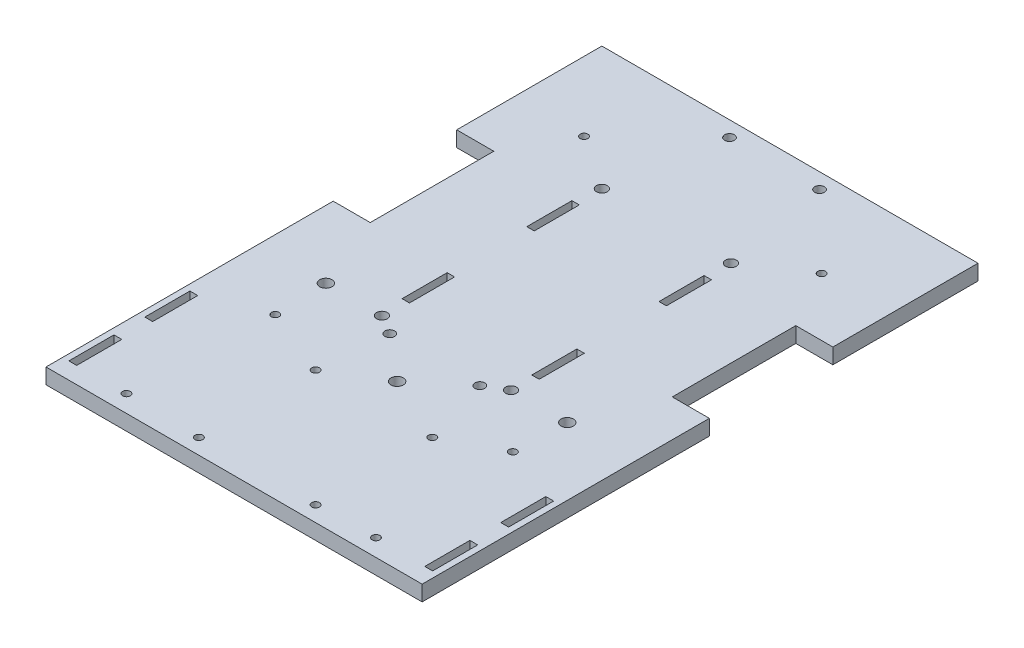
SolidWorks part; units mm, degrees
ref_plane "Front Plane" through (0, 0, 0) normal (0, 0, 1) x (1, 0, 0)
ref_plane "Top Plane" through (0, 0, 0) normal (0, 1, 0) x (1, 0, 0)
ref_plane "Right Plane" through (0, 0, 0) normal (1, 0, 0) x (0, 0, -1)
sketch "Sketch1" plane through (0, 0, 0) normal (0, 1, 0) x (1, 0, 0)
  circle A0 centre (0, 90.4441) radius 2.2225
  circle A1 centre (53.086, 90.4441) radius 2.2225
  circle A2 centre (0, 0) radius 2.2225
  circle A3 centre (53.086, 0) radius 2.2225
  dimension "D1" = 4.445
  dimension "D2" = 4.445
  dimension "D3" = 4.445
  dimension "D4" = 4.445
  dimension "D5" = 53.086
  dimension "D6" = 90.4441
  dimension "D7" = 104.8725
  dimension "D8" = 0
  dimension "D10" = 104.8725
  dimension "D11" = 53.086
  dimension "D9" = 53.086
sketch "Sketch2" plane through (0, 0, 0) normal (0, 1, 0) x (1, 0, 0)
  line L1 (-50.8, 141.2441) -> (103.886, 141.2441)
  line L2 (-50.8, 141.2441) -> (-50.8, -87.3559)
  line L3 (-50.8, -87.3559) -> (103.886, -87.3559)
  line L4 (103.886, 141.2441) -> (103.886, -87.3559)
  circle A0 centre (0, 90.4441) radius 2.2225 construction
  circle A1 centre (53.086, 90.4441) radius 2.2225 construction
  dimension "D3" = 50.8
  dimension "D1" = 50.8
  dimension "D2" = 50.8
  dimension "D4" = 228.6
extrude "Boss-Extrude1" add sketch "Sketch2" along normal blind 6.35
extrude "Cut-Extrude1" cut sketch "Sketch1" along normal blind 6.35
sketch "Sketch3" plane through (0, 6.35, 0) normal (0, 1, 0) x (1, 0, 0)
  line L0 (103.886, -87.3559) -> (103.886, 141.2441) construction
  line L1 (103.886, 81.5541) -> (88.646, 81.5541)
  line L2 (103.886, 81.5541) -> (103.886, 30.7541)
  line L3 (103.886, 30.7541) -> (88.646, 30.7541)
  line L4 (88.646, 81.5541) -> (88.646, 30.7541)
  line L5 (-50.8, 141.2441) -> (-50.8, -87.3559) construction
  line L6 (-50.8, 81.5541) -> (-35.56, 81.5541)
  line L7 (-50.8, 81.5541) -> (-50.8, 30.7541)
  line L8 (-50.8, 30.7541) -> (-35.56, 30.7541)
  line L9 (-35.56, 81.5541) -> (-35.56, 30.7541)
  circle A0 centre (0, 90.4441) radius 2.2225 construction
  point P12 (96.266, 81.5541)
  dimension "D1" = 15.24
  dimension "D2" = 15.24
  dimension "D3" = 0
  dimension "D4" = 50.8
  dimension "D5" = 50.8
  dimension "D6" = 8.89
extrude "Cut-Extrude2" cut sketch "Sketch3" against normal blind 6.35
sketch "Sketch8" plane through (0, 6.35, 0) normal (0, 1, 0) x (1, 0, 0)
  circle A0 centre (26.5501, -20.2997) radius 2.54
  circle A1 centre (-23.0771, 0.0203) radius 2.54
  circle A2 centre (76.1773, 0.0203) radius 2.54
  dimension "D1" = 5.08
  dimension "D2" = 5.08
  dimension "D3" = 5.08
  dimension "D4" = 49.6272
  dimension "D5" = 20.32
  dimension "D6" = 49.6272
  dimension "D7" = 20.32
  dimension "D9" = 26.5501
  dimension "D8" = 20.2997
extrude "Cut-Extrude3" cut sketch "Sketch8" against normal blind 17.78
sketch "Sketch9" plane through (0, 6.35, 0) normal (0, 1, 0) x (1, 0, 0)
  line L0 (29.7251, -13.9559) -> (29.7251, -121.9059)
  line L1 (-50.8, -87.3559) -> (103.886, -87.3559) construction
  circle A0 centre (53.7221, -33.0059) radius 1.5875
  circle A1 centre (53.7221, -81.0059) radius 1.5875
  circle A2 centre (5.7221, -81.0059) radius 1.5875
  circle A3 centre (5.7221, -33.0059) radius 1.5875
  circle A5 centre (26.5501, -20.2997) radius 2.54 construction
  dimension "D1" = 48
  dimension "D2" = 48
  dimension "D3" = 48
  dimension "D4" = 48
  dimension "D5" = 3.175
  dimension "D6" = 3.175
  dimension "D7" = 3.175
  dimension "D8" = 3.175
  dimension "D9" = 24.003
  dimension "D10" = 6.35
  dimension "D11" = 0
  dimension "D12" = 0
  dimension "D14" = 107.95
  dimension "D13" = 3.175
  dimension "D15" = 13.9559
extrude "Cut-Extrude4" cut sketch "Sketch9" against normal blind 17.78 contours A0 | A3 | A1 | A2
sketch "Sketch10" plane through (0, 6.35, 0) normal (0, 1, 0) x (1, 0, 0)
  circle A0 centre (-22.3266, 105.4301) radius 1.5875
  circle A1 centre (0, 90.4441) radius 2.2225 construction
  circle A2 centre (-22.3266, -21.5699) radius 1.5875
  circle A3 centre (75.4126, 105.4301) radius 1.5875
  circle A4 centre (53.086, 90.4441) radius 2.2225 construction
  circle A5 centre (75.4126, -21.5699) radius 1.5875
  dimension "D1" = 3.175
  dimension "D2" = 22.3266
  dimension "D3" = 14.986
  dimension "D4" = 3.175
  dimension "D5" = 127
  dimension "D6" = 0
  dimension "D7" = 3.175
  dimension "D8" = 14.986
  dimension "D9" = 22.3266
  dimension "D10" = 3.175
  dimension "D11" = 127
  dimension "D12" = 0
extrude "Cut-Extrude5" cut sketch "Sketch10" against normal blind 10.16
sketch "Sketch12" plane through (0, 6.35, 0) normal (0, 1, 0) x (1, 0, 0)
  line L1 (-1.8979, 10.1801) -> (1.1501, 10.1801)
  line L2 (-1.8979, 10.1801) -> (-1.8979, 28.7221)
  line L3 (-1.8979, 28.7221) -> (1.1501, 28.7221)
  line L4 (1.1501, 10.1801) -> (1.1501, 28.7221)
  line L5 (-1.8979, 61.4881) -> (1.1501, 61.4881)
  line L6 (-1.8979, 61.4881) -> (-1.8979, 80.0301)
  line L7 (-1.8979, 80.0301) -> (1.1501, 80.0301)
  line L8 (1.1501, 61.4881) -> (1.1501, 80.0301)
  line L9 (51.9501, 80.5381) -> (54.9981, 80.5381)
  line L10 (51.9501, 80.5381) -> (51.9501, 61.9961)
  line L11 (51.9501, 61.9961) -> (54.9981, 61.9961)
  line L12 (54.9981, 80.5381) -> (54.9981, 61.9961)
  line L13 (51.9501, 28.2141) -> (54.9981, 28.2141)
  line L14 (51.9501, 28.2141) -> (51.9501, 9.6721)
  line L15 (51.9501, 9.6721) -> (54.9981, 9.6721)
  line L16 (54.9981, 28.2141) -> (54.9981, 9.6721)
  circle A0 centre (26.5501, -20.2997) radius 2.54 construction
  circle A1 centre (-22.3266, 105.4301) radius 1.5875 construction
  circle A2 centre (-22.3266, -21.5699) radius 1.5875 construction
  dimension "D1" = 3.048
  dimension "D2" = 3.048
  dimension "D3" = 18.542
  dimension "D4" = 18.542
  dimension "D5" = 25.4
  dimension "D6" = 0
  dimension "D7" = 25.4
  dimension "D8" = 31.75
  dimension "D9" = 18.542
  dimension "D10" = 18.542
  dimension "D11" = 3.048
  dimension "D12" = 3.048
  dimension "D13" = 50.8
  dimension "D14" = 50.8
  dimension "D15" = 19.05
  dimension "D16" = 19.05
extrude "Cut-Extrude7" cut sketch "Sketch12" against normal blind 8.255
sketch "Sketch13" plane through (0, 6.35, 0) normal (0, 1, 0) x (1, 0, 0)
  line L0 (-50.8, 30.7541) -> (-50.8, -87.3559) construction
  line L1 (-48.26, -30.7139) -> (-45.0342, -30.7139)
  line L2 (-48.26, -30.7139) -> (-48.26, -49.2559)
  line L3 (-48.26, -49.2559) -> (-45.0342, -49.2559)
  line L4 (-45.0342, -30.7139) -> (-45.0342, -49.2559)
  line L5 (-50.8, -87.3559) -> (103.886, -87.3559) construction
  line L6 (-48.26, -61.9559) -> (-45.0342, -61.9559)
  line L7 (-48.26, -61.9559) -> (-48.26, -80.4979)
  line L8 (-48.26, -80.4979) -> (-45.0342, -80.4979)
  line L9 (-45.0342, -61.9559) -> (-45.0342, -80.4979)
  line L10 (26.543, -87.3559) -> (26.543, -125.7772) construction
  line L11 (98.1202, -61.9559) -> (98.1202, -80.4979)
  line L12 (101.346, -80.4979) -> (98.1202, -80.4979)
  line L13 (101.346, -61.9559) -> (101.346, -80.4979)
  line L14 (101.346, -61.9559) -> (98.1202, -61.9559)
  line L15 (98.1202, -30.7139) -> (98.1202, -49.2559)
  line L16 (101.346, -49.2559) -> (98.1202, -49.2559)
  line L17 (101.346, -30.7139) -> (101.346, -49.2559)
  line L18 (101.346, -30.7139) -> (98.1202, -30.7139)
  dimension "D1" = 3.2258
  dimension "D2" = 18.542
  dimension "D3" = 2.54
  dimension "D4" = 38.1
  dimension "D5" = 3.2258
  dimension "D6" = 18.542
  dimension "D7" = 2.54
  dimension "D8" = 12.7
extrude "Cut-Extrude8" cut sketch "Sketch13" against normal through all
sketch "Sketch14" plane through (0, 6.35, 0) normal (0, 1, 0) x (1, 0, 0)
  line L0 (26.543, -87.3559) -> (26.543, -107.5992) construction
  line L1 (-50.8, -87.3559) -> (103.886, -87.3559) construction
  circle A0 centre (-24.765, -80.3093) radius 1.5875
  circle A1 centre (77.851, -80.3093) radius 1.5875
extrude "Cut-Extrude9" cut sketch "Sketch14" against normal through all
sketch "Sketch16" plane through (0, 6.35, 0) normal (0, 1, 0) x (1, 0, 0)
  circle A0 centre (45.0601, 134.8941) radius 2
  circle A1 centre (8.0401, 134.8941) radius 2
  circle A2 centre (8.0401, -4.8059) radius 2
  circle A3 centre (45.0601, -4.8059) radius 2
extrude "Cut-Extrude11" cut sketch "Sketch16" against normal through all
